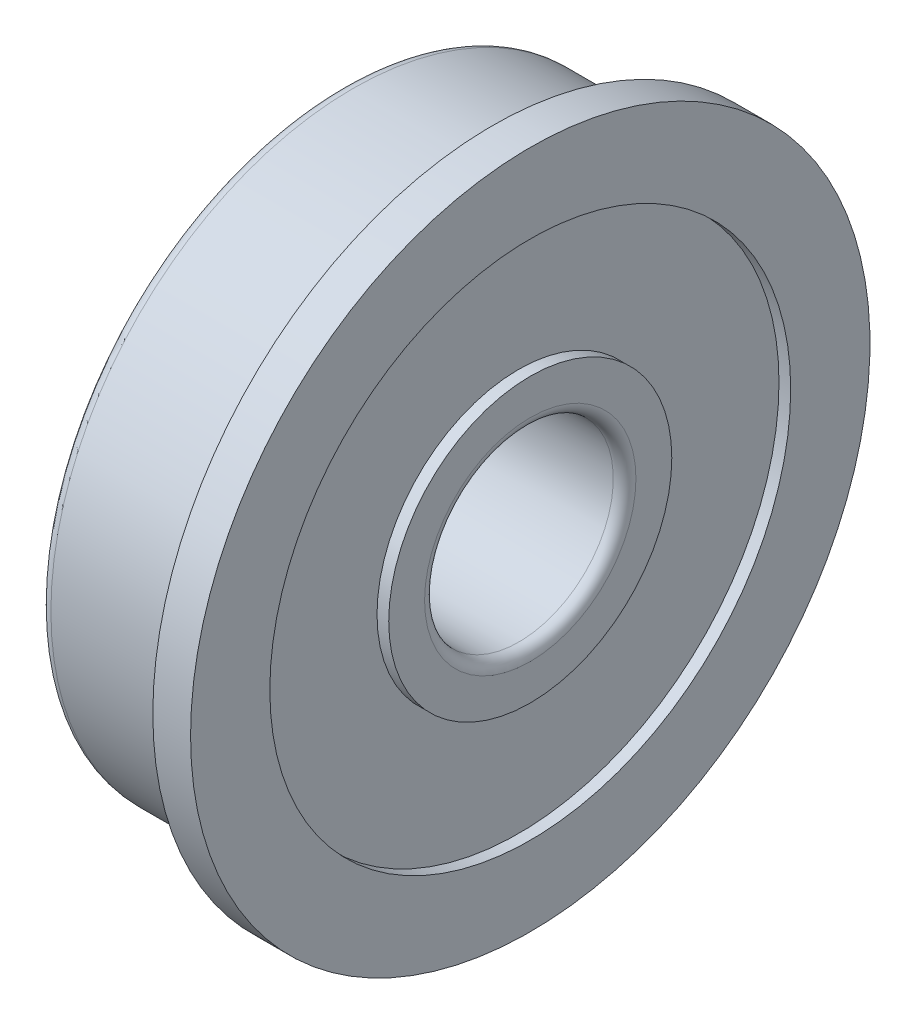
SolidWorks part; units mm, degrees
ref_plane "Front Plane" through (0, 0, 0) normal (0, 0, 1) x (1, 0, 0)
ref_plane "Top Plane" through (0, 0, 0) normal (0, 1, 0) x (1, 0, 0)
ref_plane "Right Plane" through (0, 0, 0) normal (1, 0, 0) x (0, 0, -1)
sketch "Sketch1" plane through (0, 0, 0) normal (0, 0, 1) x (1, 0, 0)
  line L0 (-4, 0) -> (1, 0) construction
  line L1 (0, 8.2) -> (0, 9)
  line L2 (0, 9) -> (1, 9)
  line L3 (1, 9) -> (1, 6.9)
  line L4 (1, 2.5) -> (-4, 2.5)
  line L5 (-4, 2.5) -> (-4, 3.75)
  line L6 (-4, 8) -> (-0.2, 8)
  line L7 (-4, 6.9) -> (-3.69, 6.9)
  line L8 (-3.69, 6.9) -> (-3.69, 3.75)
  line L9 (-3.69, 3.75) -> (-4, 3.75)
  line L10 (1, 6.9) -> (0.69, 6.9)
  line L11 (0.69, 6.9) -> (0.69, 3.75)
  line L12 (0.69, 3.75) -> (1, 3.75)
  line L13 (-4, 6.9) -> (-4, 8)
  line L14 (1, 3.75) -> (1, 2.5)
  arc A0 (-0.2, 8) -> (0, 8.2) centre (0, 8) ccw
  dimension "FIX_1" = 0.2
  dimension "D_s" = 5
  dimension "C" = 1
  dimension "MSM_2" = 7.5
  dimension "MSM_1" = 13.8
  dimension "D" = 16
  dimension "D1." = 18
  dimension "B" = 5
  dimension "MSM_3" = 0.31
revolve "Revolve1" add sketch "Sketch1" angle 360 about L0
fillet "Fillet1" radius 0.3 3 edges at (1, 0, 2.5) (-4, 0, 2.5) (-4, 0, 8)
